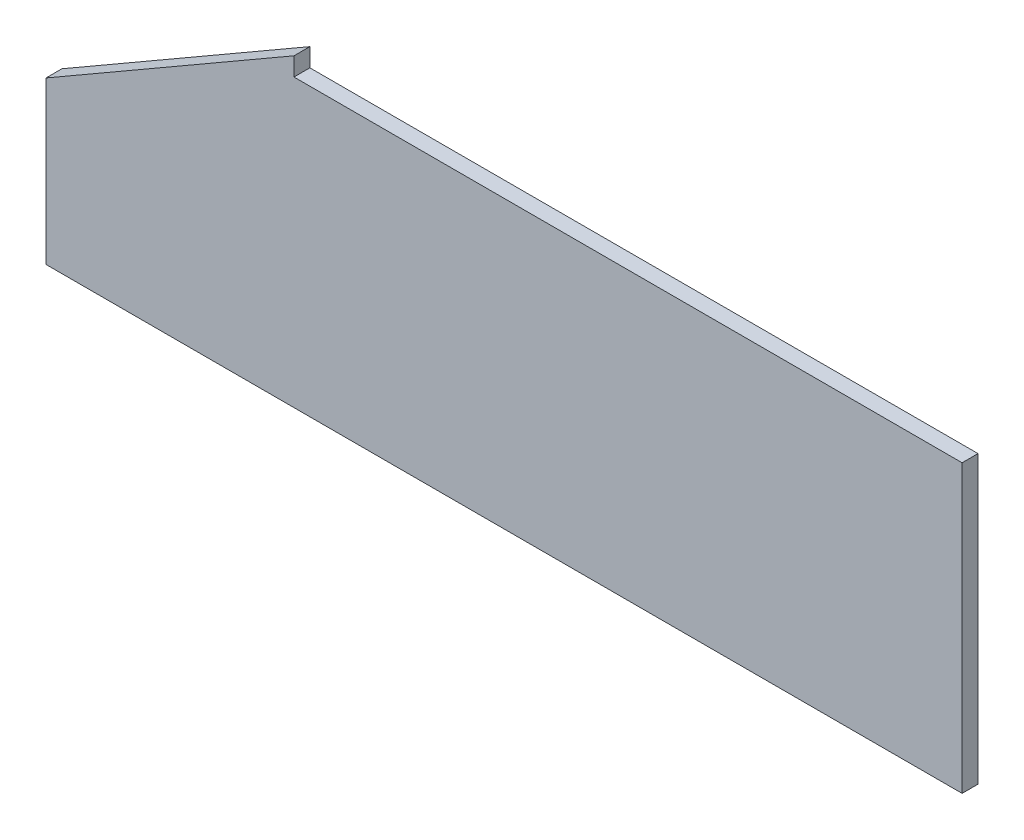
SolidWorks part; units mm, degrees
ref_plane "Front Plane" through (0, 0, 0) normal (0, 0, 1) x (1, 0, 0)
ref_plane "Top Plane" through (0, 0, 0) normal (0, 1, 0) x (1, 0, 0)
ref_plane "Right Plane" through (0, 0, 0) normal (1, 0, 0) x (0, 0, -1)
sketch "Sketch3" plane through (0, 0, 0) normal (0, 0, 1) x (1, 0, 0)
  line L0 (0, 101.55) -> (155.8846, 191.55)
  line L1 (0, 0) -> (575.8846, 0)
  line L3 (0, 101.55) -> (0, 0)
  line L5 (155.8846, 191.55) -> (155.8846, 180)
  line L6 (155.8846, 180) -> (575.8846, 180)
  line L7 (575.8846, 180) -> (575.8846, 0)
  dimension "D1" = 11.55
  dimension "D2" = 180
  dimension "D3" = 180
  dimension "D4" = 420
  dimension "D5" = 60
extrude "Extrude1" add sketch "Sketch3" along normal blind 10
